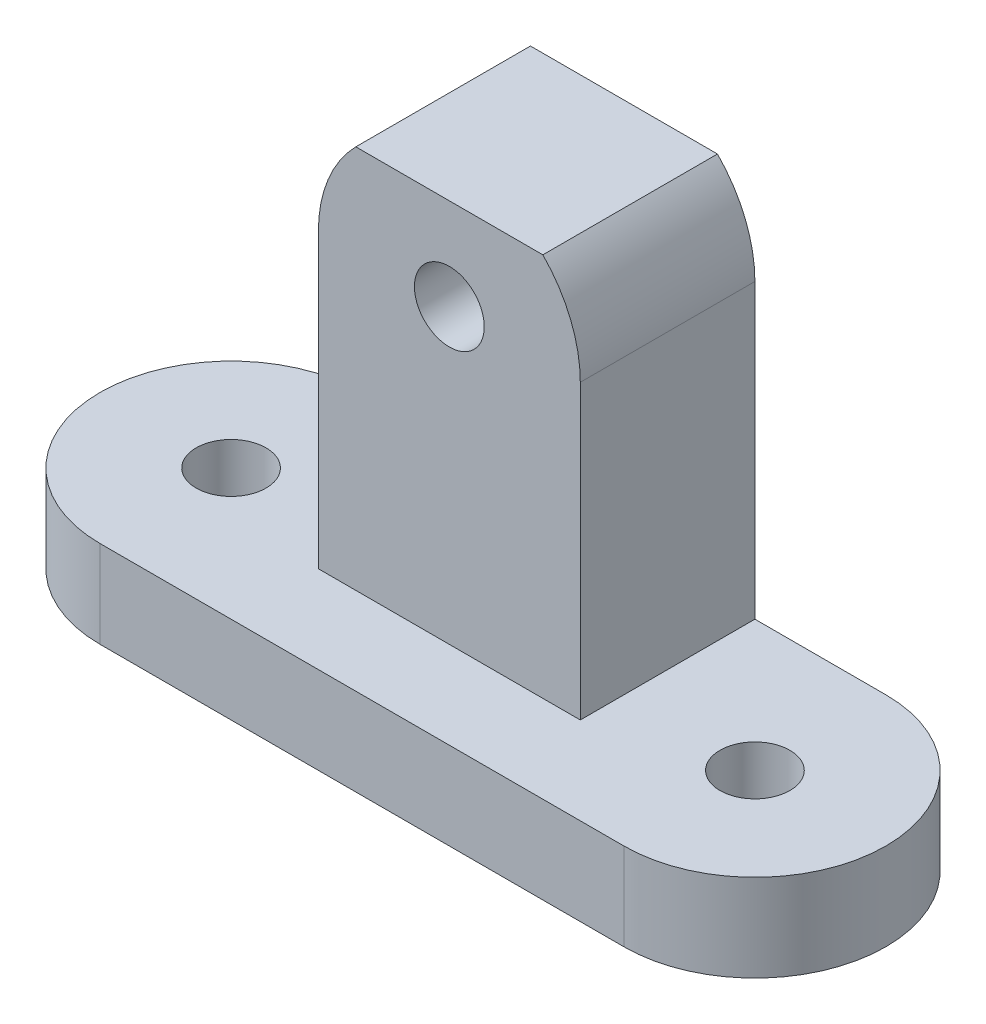
SolidWorks part; units mm, degrees
ref_plane "Front Plane" through (0, 0, 0) normal (0, 0, 1) x (1, 0, 0)
ref_plane "Top Plane" through (0, 0, 0) normal (0, 1, 0) x (1, 0, 0)
ref_plane "Right Plane" through (0, 0, 0) normal (1, 0, 0) x (0, 0, -1)
sketch "Sketch1" plane through (0, 0, 0) normal (0, 1, 0) x (1, 0, 0)
  line L1 (0, 0) -> (30, 0)
  line L2 (0, 0) -> (0, 15) construction
  line L3 (0, 15) -> (30, 15)
  line L4 (30, 0) -> (30, 15) construction
  arc A0 (0, 15) -> (0, 0) centre (0, 7.5) ccw
  arc A1 (30, 15) -> (30, 0) centre (30, 7.5) cw
  circle A2 centre (0, 7.5) radius 2
  circle A4 centre (30, 7.5) radius 2
  dimension "D3" = 4
  dimension "D4" = 4
  dimension "D1" = 15
  dimension "D2" = 30
extrude "Boss-Extrude1" add sketch "Sketch1" along normal blind 5
sketch "Sketch3" plane through (0, 0, -15) normal (0, 0, -1) x (-1, 0, 0)
  line L0 (-30, 5) -> (0, 5) construction
  line L1 (-22.5, 5) -> (-7.5, 5)
  line L2 (-22.5, 5) -> (-22.5, 21.75)
  line L3 (-22.5, 21.75) -> (-7.5, 21.75) construction
  line L4 (-7.5, 5) -> (-7.5, 21.75)
  line L5 (-15, 21.75) -> (-15, 5) construction
  arc A0 (-22.5, 21.75) -> (-7.5, 21.75) centre (-15, 21.75) cw
  circle A1 centre (-15, 21.75) radius 2
  dimension "D1" = 4
  dimension "D2" = 15
  dimension "D3" = 16.75
extrude "Boss-Extrude2" add sketch "Sketch3" against normal blind 10
sketch "Sketch4" plane through (0, 0, -15) normal (0, 0, -1) x (-1, 0, 0)
  line L0 (-30, 0) -> (0, 0) construction
  line L1 (-25.497, 31.1953) -> (-1.3854, 31.1953)
  line L2 (-25.497, 31.1953) -> (-25.497, 27)
  line L3 (-25.497, 27) -> (-1.3854, 27)
  line L4 (-1.3854, 31.1953) -> (-1.3854, 27)
  dimension "D1" = 27
extrude "Cut-Extrude1" cut sketch "Sketch4" against normal through all
